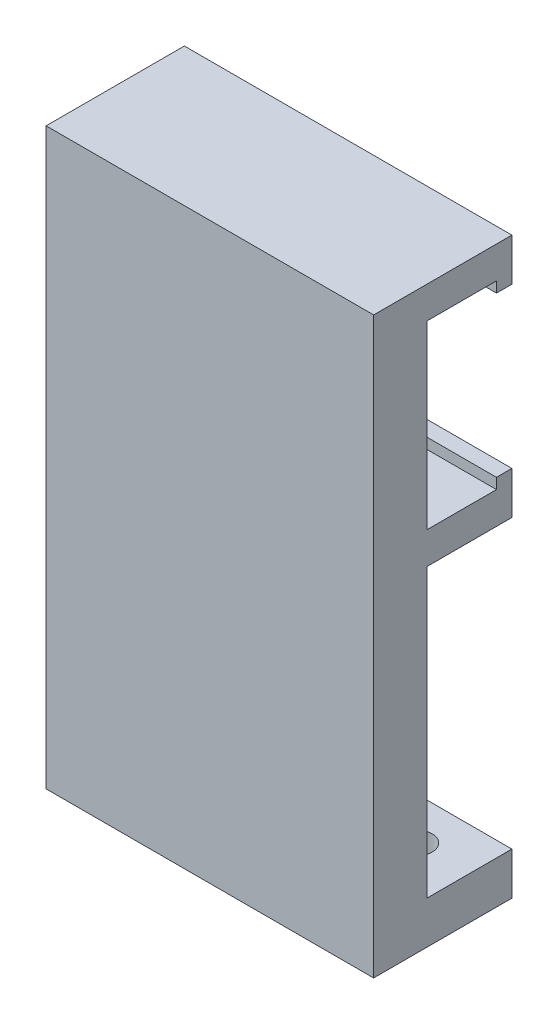
SolidWorks part; units mm, degrees
ref_plane "前视基准面" through (0, 0, 0) normal (0, 0, 1) x (1, 0, 0)
ref_plane "上视基准面" through (0, 0, 0) normal (0, 1, 0) x (1, 0, 0)
ref_plane "右视基准面" through (0, 0, 0) normal (1, 0, 0) x (0, 0, -1)
sketch "草图1" plane through (0, 0, 0) normal (0, 0, 1) x (1, 0, 0)
  line L1 (-15.4, 27) -> (15.4, 27)
  line L2 (-15.4, 27) -> (-15.4, -27)
  line L3 (-15.4, -27) -> (15.4, -27)
  line L4 (15.4, 27) -> (15.4, -27)
  line L5 (-15.4, 27) -> (15.4, -27) construction
  line L6 (-15.4, -27) -> (15.4, 27) construction
  point P0 (0, 0)
  dimension "D1" = 30.8
  dimension "D2" = 54
extrude "凸台-拉伸1" add sketch "草图1" along normal blind 5
sketch "草图2" plane through (0, 0, 0) normal (0, 0, -1) x (-1, 0, 0)
  line L0 (-15.4, -27) -> (-15.4, 27) construction
  line L1 (15.4, -27) -> (-15.4, -27)
  line L2 (15.4, -27) -> (15.4, -23)
  line L3 (15.4, -23) -> (-15.4, -23)
  line L4 (-15.4, -27) -> (-15.4, -23)
  dimension "D1" = 4
extrude "凸台-拉伸2" add sketch "草图2" along normal blind 8
sketch "草图3" plane through (0, -23, 0) normal (0, 1, 0) x (1, 0, 0)
  line L0 (15.4, 4) -> (10.4, 4) construction
  line L1 (15.4, 8) -> (15.4, 0) construction
  line L2 (-15.4, 4) -> (-10.4, 4) construction
  line L3 (-15.4, 8) -> (-15.4, 0) construction
  circle A0 centre (10.4, 4) radius 1.5
  circle A1 centre (-10.4, 4) radius 1.5
  dimension "D2" = 5
  dimension "D1" = 5
extrude "切除-拉伸1" cut sketch "草图3" against normal through all
sketch "草图4" plane through (0, 0, 0) normal (0, 0, -1) x (-1, 0, 0)
  line L6 (15.4, 27) -> (15.4, -23) construction
  line L7 (-15.4, 27) -> (15.4, 27)
  line L8 (-15.4, 27) -> (-15.4, 24)
  line L9 (-15.4, 24) -> (15.4, 24)
  line L10 (15.4, 27) -> (15.4, 24)
  line L11 (-15.4, 24) -> (-15.4, 7) construction
  line L12 (-15.4, -23) -> (-15.4, 27) construction
  line L14 (-15.4, 7) -> (15.4, 7)
  line L15 (-15.4, 7) -> (-15.4, 4)
  line L16 (-15.4, 4) -> (15.4, 4)
  line L17 (15.4, 7) -> (15.4, 4)
  dimension "D1" = 3
  dimension "D2" = 17
  dimension "D3" = 3
extrude "凸台-拉伸3" add sketch "草图4" along normal blind 8
sketch "草图5" plane through (0, 7, 0) normal (0, 1, 0) x (1, 0, 0)
  line L0 (-15.4, 8) -> (-15.4, 0) construction
  line L1 (15.4, 8) -> (-15.4, 8)
  line L2 (15.4, 8) -> (15.4, 6.55)
  line L3 (15.4, 6.55) -> (-15.4, 6.55)
  line L4 (-15.4, 8) -> (-15.4, 6.55)
  dimension "D1" = 1.45
extrude "凸台-拉伸4" add sketch "草图5" along normal blind 1
sketch "草图6" plane through (0, 24, 0) normal (0, -1, 0) x (1, 0, 0)
  line L0 (-15.4, -8) -> (-15.4, 0) construction
  line L1 (15.4, -8) -> (-15.4, -8)
  line L2 (15.4, -8) -> (15.4, -6.55)
  line L3 (15.4, -6.55) -> (-15.4, -6.55)
  line L4 (-15.4, -8) -> (-15.4, -6.55)
  dimension "D1" = 1.45
extrude "凸台-拉伸5" add sketch "草图6" along normal blind 1
sketch "草图7" plane through (0, 0, 0) normal (0, 0, -1) x (-1, 0, 0)
  line L0 (0, 4) -> (0, -7) construction
  line L2 (-15.4, 4) -> (15.4, 4) construction
  line L8 (-2.5, -18) -> (2.5, -18)
  line L9 (-2.5, -18) -> (-2.5, 4)
  line L10 (-2.5, 4) -> (2.5, 4)
  line L11 (2.5, -18) -> (2.5, 4)
  line L12 (-2.5, -18) -> (2.5, 4) construction
  line L13 (-2.5, 4) -> (2.5, -18) construction
  point P5 (-1.2452, 4)
  dimension "D1" = 11
  dimension "D2" = 5
extrude "凸台-拉伸6" add sketch "草图7" along normal blind 8
